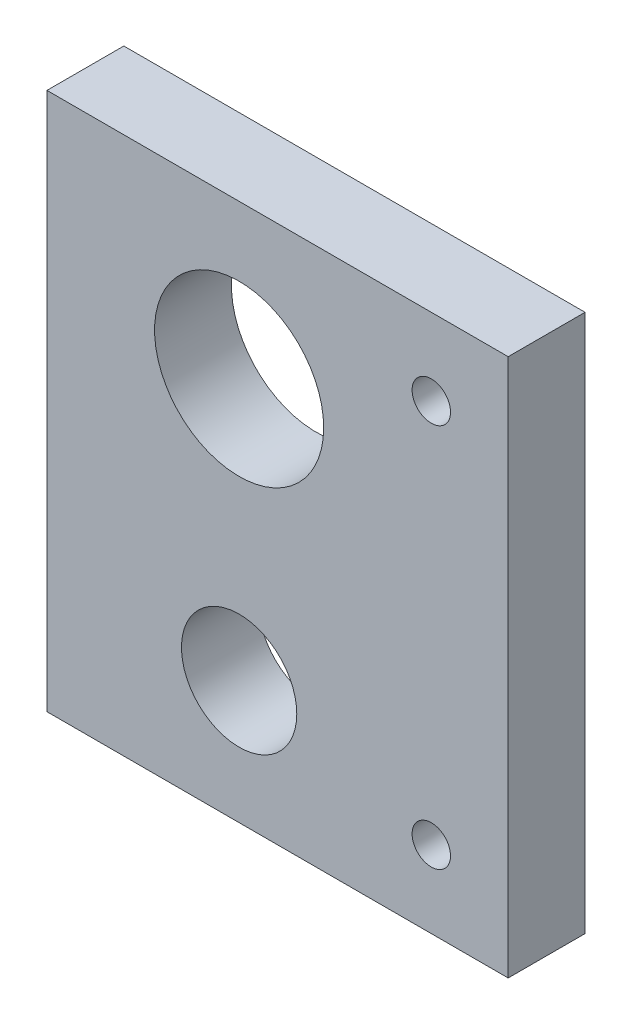
SolidWorks part; units mm, degrees
material "Alloy Steel"
ref_plane "Front Plane" through (0, 0, 0) normal (0, 0, 1) x (1, 0, 0)
ref_plane "Top Plane" through (0, 0, 0) normal (0, 1, 0) x (1, 0, 0)
ref_plane "Right Plane" through (0, 0, 0) normal (1, 0, 0) x (0, 0, -1)
sketch "Sketch1" plane through (0, 0, 0) normal (0, 0, 1) x (1, 0, 0)
  line L0 (-5, 35) -> (-5, -35) construction
  line L1 (-30, -35) -> (30, -35)
  line L2 (-30, -35) -> (-30, 35)
  line L3 (-30, 35) -> (30, 35)
  line L4 (30, -35) -> (30, 35)
  line L5 (-30, -35) -> (30, 35) construction
  line L6 (-30, 35) -> (30, -35) construction
  line L7 (20, 35) -> (20, -35) construction
  circle A0 centre (-5, 15) radius 11
  circle A1 centre (-5, -19) radius 7.5
  circle A2 centre (20, 25) radius 2.5
  circle A3 centre (20, -25) radius 2.5
  point P0 (0, 0)
  dimension "D3" = 22
  dimension "D4" = 15
  dimension "D7" = 5
  dimension "D8" = 5
  dimension "D1" = 60
  dimension "D2" = 70
  dimension "D5" = 25
  dimension "D6" = 25
  dimension "D9" = 10
  dimension "D10" = 10
  dimension "D11" = 20
  dimension "D12" = 16
extrude "Boss-Extrude1" add sketch "Sketch1" along normal blind 10
